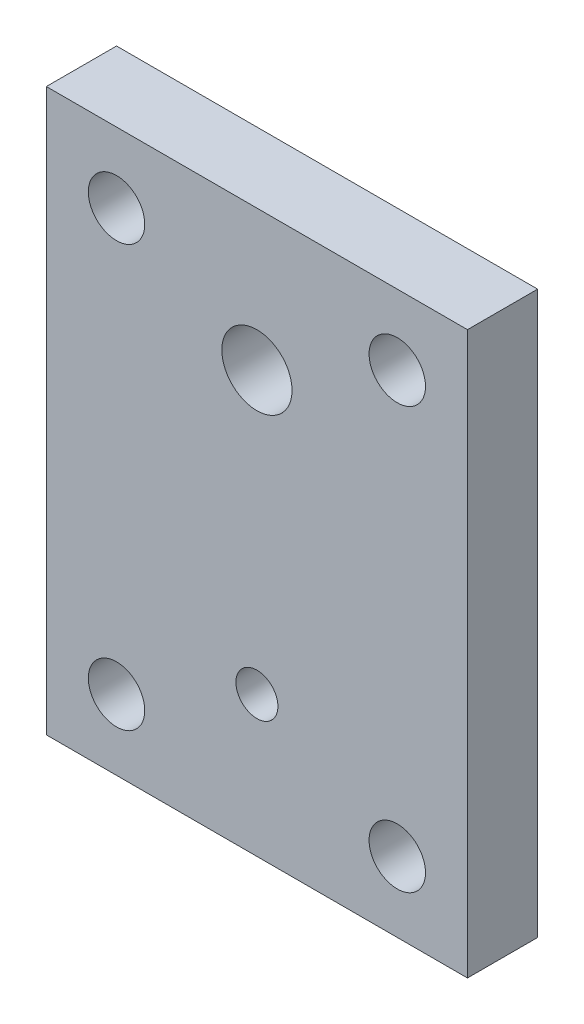
SolidWorks part; units mm, degrees
material "ABS PC"
ref_plane "Front Plane" through (0, 0, 0) normal (0, 0, 1) x (1, 0, 0)
ref_plane "Top Plane" through (0, 0, 0) normal (0, 1, 0) x (1, 0, 0)
ref_plane "Right Plane" through (0, 0, 0) normal (1, 0, 0) x (0, 0, -1)
sketch "Sketch3" plane through (0, 0, 0) normal (0, 0, 1) x (1, 0, 0)
  line L0 (6.35, 44.45) -> (31.75, 44.45) construction
  line L1 (0, 0) -> (38.1, 0)
  line L2 (0, 0) -> (0, 50.8)
  line L3 (0, 50.8) -> (38.1, 50.8)
  line L4 (38.1, 0) -> (38.1, 50.8)
  line L5 (31.75, 44.45) -> (31.75, 6.35) construction
  line L6 (31.75, 6.35) -> (6.35, 6.35) construction
  line L7 (6.35, 6.35) -> (6.35, 44.45) construction
  circle A0 centre (6.35, 44.45) radius 2.5527
  circle A1 centre (31.75, 44.45) radius 2.5527
  circle A2 centre (31.75, 6.35) radius 2.5527
  circle A3 centre (6.35, 6.35) radius 2.5527
  circle A4 centre (19.05, 38.1) radius 3.175
  circle A5 centre (19.05, 12.7) radius 1.8986
  dimension "D7" = 5.1054
  dimension "D8" = 5.1054
  dimension "D9" = 5.1054
  dimension "D10" = 5.1054
  dimension "D13" = 6.35
  dimension "D16" = 3.7973
  dimension "D1" = 38.1
  dimension "D2" = 50.8
  dimension "D3" = 6.35
  dimension "D4" = 6.35
  dimension "D5" = 6.35
  dimension "D6" = 6.35
  dimension "D11" = 19.05
  dimension "D12" = 12.7
  dimension "D14" = 19.05
  dimension "D15" = 12.7
extrude "Boss-Extrude4" add sketch "Sketch3" along normal blind 6.35
